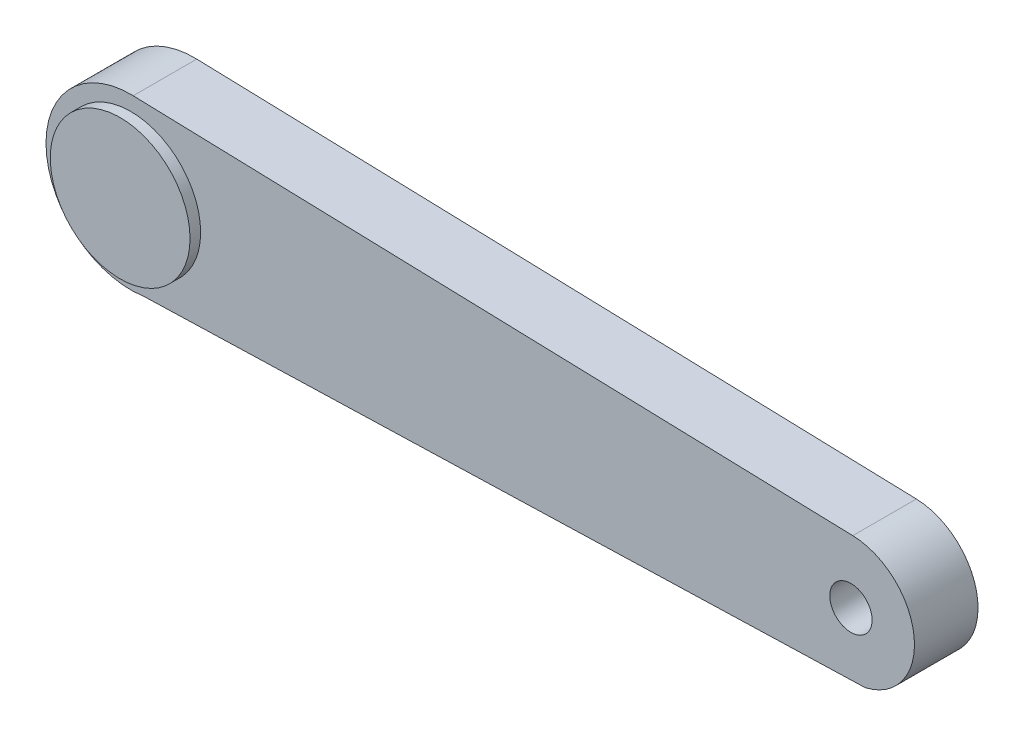
SolidWorks part; units mm, degrees
ref_plane "Front Plane" through (0, 0, 0) normal (0, 0, 1) x (1, 0, 0)
ref_plane "Top Plane" through (0, 0, 0) normal (0, 1, 0) x (1, 0, 0)
ref_plane "Right Plane" through (0, 0, 0) normal (1, 0, 0) x (0, 0, -1)
sketch "Sketch1" plane through (0, 0, 0) normal (0, 0, 1) x (1, 0, 0)
  line L0 (0, 0) -> (-85, 0)
  line L1 (0, 0) -> (85, 0)
  line L2 (-84.4118, 19.9913) -> (85.4412, 14.9935)
  line L3 (-81.9839, -19.7713) -> (88.3501, -14.6211)
  circle A0 centre (-85, 0) radius 20
  circle A1 centre (85, 0) radius 15
  dimension "D3" = 40
  dimension "D4" = 30
  dimension "D1" = 85
  dimension "D2" = 85
extrude "Boss-Extrude1" add sketch "Sketch1" along normal mid plane 15
sketch "Sketch3" plane through (0, 0, 7.5) normal (0, 0, 1) x (1, 0, 0)
  circle A0 centre (-85, 0) radius 16.5
  dimension "D1" = 33
extrude "Boss-Extrude2" add sketch "Sketch3" along normal mid plane 5 contours A0
sketch "Sketch6" plane through (0, 0, 7.5) normal (0, 0, 1) x (1, 0, 0)
  circle A0 centre (85, 0) radius 5
  dimension "D1" = 10
extrude "Cut-Extrude1" cut sketch "Sketch6" against normal blind 10
sketch "Sketch7" plane through (0, 0, -7.5) normal (0, 0, -1) x (-1, 0, 0)
  circle A0 centre (85, 0) radius 5
  dimension "D1" = 10
extrude "Boss-Extrude3" add sketch "Sketch7" along normal blind 10
